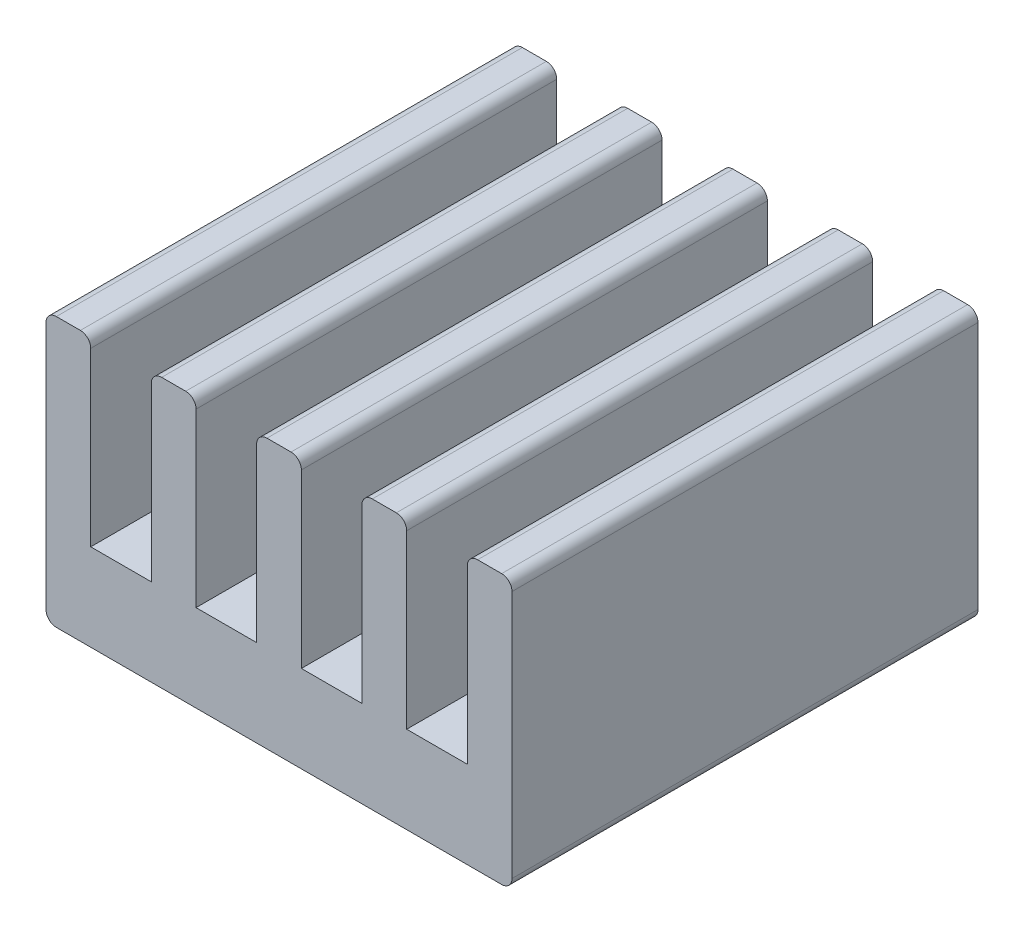
SolidWorks part; units mm, degrees
material "Lega 1060"
ref_plane "Piano frontale" through (0, 0, 0) normal (0, 0, 1) x (1, 0, 0)
ref_plane "Piano superiore" through (0, 0, 0) normal (0, 1, 0) x (1, 0, 0)
ref_plane "Piano destro" through (0, 0, 0) normal (1, 0, 0) x (0, 0, -1)
sketch "Schizzo1" plane through (0, 0, 0) normal (0, 1, 0) x (1, 0, 0)
  line L1 (-4.5, -4.5) -> (4.5, -4.5)
  line L2 (-4.5, -4.5) -> (-4.5, 4.5)
  line L3 (-4.5, 4.5) -> (4.5, 4.5)
  line L4 (4.5, -4.5) -> (4.5, 4.5)
  line L5 (-4.5, -4.5) -> (4.5, 4.5) construction
  line L6 (-4.5, 4.5) -> (4.5, -4.5) construction
  point P0 (0, 0)
  dimension "D1" = 9
  dimension "D2" = 9
extrude "Estrusione-Estrusione1" add sketch "Schizzo1" along normal blind 5.2
sketch "Schizzo2" plane through (0, 0, 4.5) normal (0, 0, 1) x (1, 0, 0)
  line L0 (-4.5, 5.2) -> (4.5, 5.2) construction
  line L1 (-3.636, 5.2) -> (-2.466, 5.2)
  line L2 (-3.636, 5.2) -> (-3.636, 1.68)
  line L3 (-3.636, 1.68) -> (-2.466, 1.68)
  line L4 (-2.466, 5.2) -> (-2.466, 1.68)
  line L5 (-4.5, 0) -> (4.5, 0) construction
  line L6 (0.432, 5.2) -> (1.602, 5.2)
  line L7 (0.432, 5.2) -> (0.432, 1.68)
  line L8 (0.432, 1.68) -> (1.602, 1.68)
  line L9 (1.602, 5.2) -> (1.602, 1.68)
  line L10 (2.466, 5.2) -> (3.636, 5.2)
  line L11 (2.466, 5.2) -> (2.466, 1.68)
  line L12 (2.466, 1.68) -> (3.636, 1.68)
  line L13 (3.636, 5.2) -> (3.636, 1.68)
  line L14 (-1.602, 5.2) -> (-0.432, 5.2)
  line L15 (-1.602, 5.2) -> (-1.602, 1.68)
  line L16 (-1.602, 1.68) -> (-0.432, 1.68)
  line L17 (-0.432, 5.2) -> (-0.432, 1.68)
  line L21 (-4.5, 5.2) -> (-4.5, 0) construction
  dimension "D1" = 1.68
  dimension "D2" = 1.17
  dimension "D3" = 1.17
  dimension "D4" = 1.17
  dimension "D5" = 1.17
  dimension "D6" = 0.864
  dimension "D7" = 0.864
  dimension "D8" = 0.864
  dimension "D9" = 0.864
extrude "Taglio-Estrusione1" cut sketch "Schizzo2" against normal through all
fillet "Raccordo1" radius 0.2 12 edges at (-4.5, 5.2, 0) (-3.636, 5.2, 0) (-2.466, 5.2, 0) (-1.602, 5.2, 0) (-0.432, 5.2, 0) (0.432, 5.2, 0) (1.602, 5.2, 0) (2.466, 5.2, 0) (3.636, 5.2, 0) (4.5, 5.2, 0) (-4.5, 0, 0) (4.5, 0, 0)
